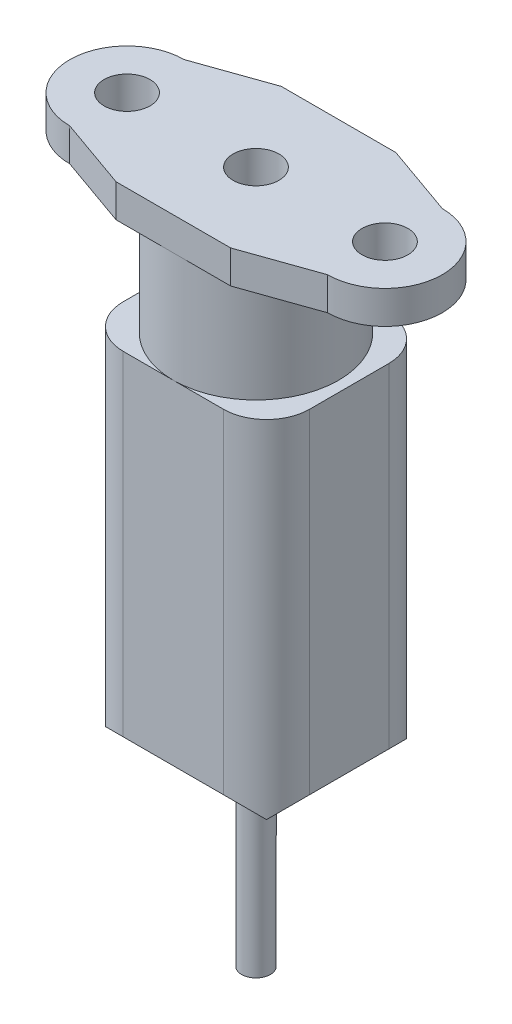
SolidWorks part; units mm, degrees
ref_plane "Front Plane" through (0, 0, 0) normal (0, 0, 1) x (1, 0, 0)
ref_plane "Top Plane" through (0, 0, 0) normal (0, 1, 0) x (1, 0, 0)
ref_plane "Right Plane" through (0, 0, 0) normal (1, 0, 0) x (0, 0, -1)
ref_plane "Plane1" through (0, -2.3, 0) normal (0, -1, 0) x (1, 0, 0)
sketch "Sketch1" plane through (0, -2.3, 0) normal (0, -1, 0) x (1, 0, 0)
  line L0 (-75.7, -20.765) -> (-67.7, -20.765)
  line L1 (-67.7, -20.765) -> (-62.7, -19)
  line L2 (-62.7, -11) -> (-67.7, -9.235)
  line L3 (-67.7, -9.235) -> (-75.7, -9.235)
  line L4 (-75.7, -9.235) -> (-80.7, -11)
  line L5 (-80.7, -19) -> (-75.7, -20.765)
  circle A0 centre (-62.7, -15) radius 1.6
  arc A1 (-62.7, -19) -> (-62.7, -11) centre (-62.7, -15) ccw
  arc A2 (-80.7, -11) -> (-80.7, -19) centre (-80.7, -15) ccw
  circle A3 centre (-71.7, -15) radius 1.6
  circle A4 centre (-80.7, -15) radius 1.6
extrude "Boss-Extrude1" add sketch "Sketch1" against normal blind 2.3
sketch "Sketch2" plane through (0, -2.3, 0) normal (0, -1, 0) x (1, 0, 0)
  circle A0 centre (-71.7, -15) radius 5.765
extrude "Boss-Extrude2" add sketch "Sketch2" along normal blind 7.7
sketch "Sketch3" plane through (0, -10, 0) normal (0, -1, 0) x (1, 0, 0)
  line L0 (-65.2, -9.235) -> (-65.2, -20.765)
  line L1 (-65.2, -20.765) -> (-78.2, -20.765)
  line L2 (-78.2, -20.765) -> (-78.2, -9.235)
  line L3 (-78.2, -9.235) -> (-65.2, -9.235)
extrude "Boss-Extrude3" add sketch "Sketch3" along normal blind 26.3
sketch "Sketch4" plane through (0, -36.3, 0) normal (0, -1, 0) x (1, 0, 0)
  circle A0 centre (-71.7, -15) radius 1
extrude "Boss-Extrude4" add sketch "Sketch4" along normal blind 12
chamfer "Chamfer1" distance 3 angle 45 4 edges at (-78.2, -36.3, -15) (-71.7, -36.3, -9.235) (-71.7, -36.3, -20.765) (-65.2, -36.3, -15)
fillet "Fillet1" radius 3 4 edges at (-78.2, -21.65, -20.765) (-78.2, -21.65, -9.235) (-65.2, -21.65, -9.235) (-65.2, -21.65, -20.765)
